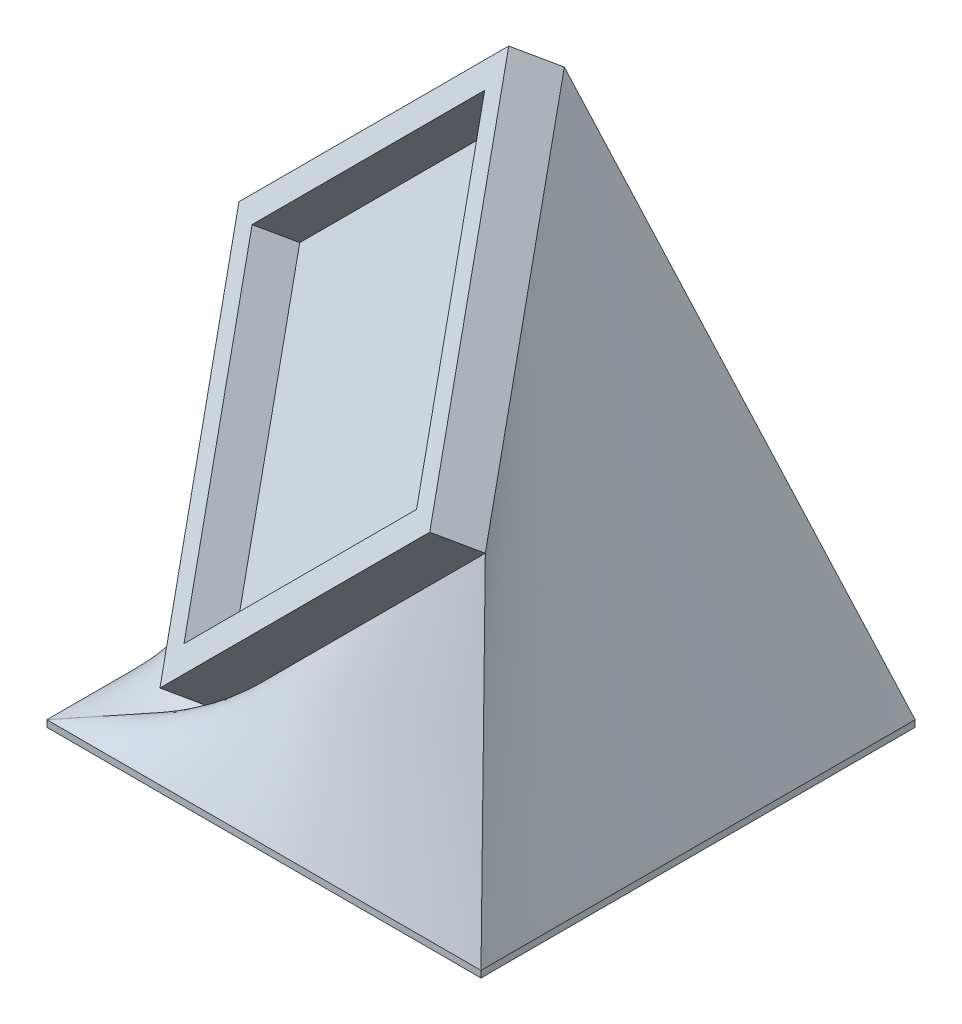
SolidWorks part; units mm, degrees
ref_plane "Front Plane" through (0, 0, 0) normal (0, 0, 1) x (1, 0, 0)
ref_plane "Top Plane" through (0, 0, 0) normal (0, 1, 0) x (1, 0, 0)
ref_plane "Right Plane" through (0, 0, 0) normal (1, 0, 0) x (0, 0, -1)
sketch "Sketch1" plane through (0, 0, 0) normal (0, 1, 0) x (1, 0, 0)
  line L1 (-22.2888, 13.0013) -> (14.5412, 13.0013)
  line L2 (-22.2888, 13.0013) -> (-22.2888, -23.8287)
  line L3 (-22.2888, -23.8287) -> (14.5412, -23.8287)
  line L4 (14.5412, 13.0013) -> (14.5412, -23.8287)
  dimension "D1" = 36.83
  dimension "D2" = 36.83
extrude "Boss-Extrude1" add sketch "Sketch1" along normal blind 0.635
sketch "Sketch2" plane through (0, 0.635, 0) normal (0, 1, 0) x (1, 0, 0)
  line L0 (14.5412, 13.0013) -> (-22.2888, 13.0013) construction
  line L1 (-19.7488, 10.4613) -> (12.0012, 10.4613)
  line L2 (-19.7488, 10.4613) -> (-19.7488, -21.2887)
  line L3 (-19.7488, -21.2887) -> (12.0012, -21.2887)
  line L4 (12.0012, 10.4613) -> (12.0012, -21.2887)
  line L5 (-22.2888, 13.0013) -> (-22.2888, -23.8287) construction
  line L7 (-22.2888, 13.0013) -> (14.5412, 13.0013)
  line L8 (-22.2888, 13.0013) -> (-22.2888, -23.8287)
  line L9 (-22.2888, -23.8287) -> (14.5412, -23.8287)
  line L10 (14.5412, 13.0013) -> (14.5412, -23.8287)
  dimension "D1" = 31.75
  dimension "D2" = 31.75
  dimension "D3" = 2.54
  dimension "D4" = 2.54
extrude "Boss-Extrude2" add sketch "Sketch2" along normal blind 3.81 contours L8 L7 L10 L9 | L2 L1 L4 L3
move or copy body "Body-Move/Copy1" bodies to move or copy 102 copy no translate (0, 20.32, 0)
sketch "Sketch3" plane through (0, 0, 0) normal (0, 1, 0) x (1, 0, 0)
  line L0 (-22.2888, 13.0013) -> (-22.2888, -23.8287) construction
  line L1 (-24.8288, 15.5413) -> (17.0812, 15.5413)
  line L2 (-24.8288, 15.5413) -> (-24.8288, -26.3687)
  line L3 (-24.8288, -26.3687) -> (17.0812, -26.3687)
  line L4 (17.0812, 15.5413) -> (17.0812, -26.3687)
  line L5 (-22.2888, -23.8287) -> (14.5412, -23.8287) construction
  dimension "D1" = 41.91
  dimension "D2" = 41.91
  dimension "D3" = 2.54
  dimension "D4" = 2.54
extrude "Boss-Extrude3" add sketch "Sketch3" along normal blind 0.635 separate body
move or copy body "Body-Move/Copy2" bodies to move or copy 103 copy no rotation origin (-5.4913, 4.0925, 3.7962) rotation axis (0.6786, 0.2811, 0.6786) rotation angle 62.799
move or copy body "Body-Move/Copy3" bodies to move or copy 105 copy no translate (0, 12.4373, -9.987)
loft "Loft1" add section face at (-11.6525, 24.9785, 6.4275) section face at (-3.8738, 0.635, 5.4137)
sketch "Sketch4" plane through (-16.0928, 16.0928, -22.7587) normal (-0.5, 0.5, -0.7071) x (0.8651, 0.3256, -0.3815)
  text T0 "45 x 45\r\n"
extrude "Cut-Extrude1" cut sketch "Sketch4" against normal blind 0.635
